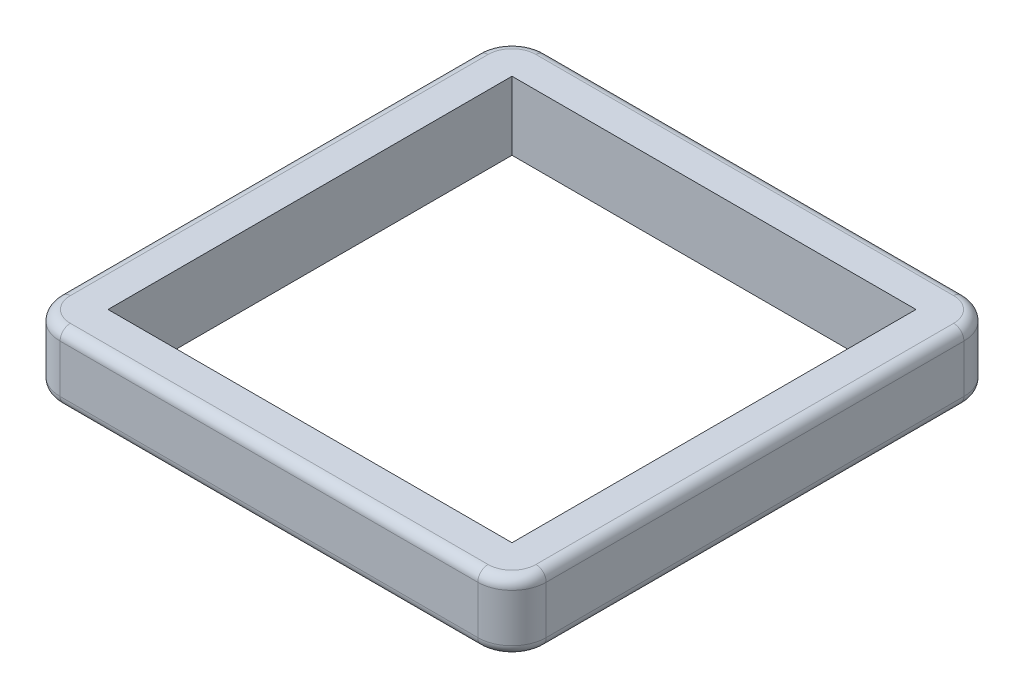
SolidWorks part; units mm, degrees
ref_plane "Front Plane" through (0, 0, 0) normal (0, 0, 1) x (1, 0, 0)
ref_plane "Top Plane" through (0, 0, 0) normal (0, 1, 0) x (1, 0, 0)
ref_plane "Right Plane" through (0, 0, 0) normal (1, 0, 0) x (0, 0, -1)
sketch "Sketch1" plane through (0, 0, 0) normal (0, 1, 0) x (1, 0, 0)
  line L0 (-450.85, 450.85) -> (450.85, 450.85)
  line L1 (-374.65, 374.65) -> (374.65, 374.65)
  line L2 (-374.65, 374.65) -> (-374.65, -374.65)
  line L3 (-374.65, -374.65) -> (374.65, -374.65)
  line L4 (374.65, 374.65) -> (374.65, -374.65)
  line L5 (-374.65, 374.65) -> (374.65, -374.65) construction
  line L6 (-374.65, -374.65) -> (374.65, 374.65) construction
  line L7 (450.85, 450.85) -> (450.85, -450.85)
  line L8 (-450.85, -450.85) -> (450.85, -450.85)
  line L9 (-450.85, 450.85) -> (-450.85, -450.85)
  point P0 (0, 0)
  dimension "D1" = 749.3
  dimension "D2" = 76.2
extrude "Boss-Extrude1" add sketch "Sketch1" along normal blind 127
fillet "Fillet1" radius 63.5 4 edges at (-450.85, 63.5, -450.85) (450.85, 63.5, -450.85) (450.85, 63.5, 450.85) (-450.85, 63.5, 450.85)
fillet "Fillet2" radius 19.05 16 edges at (432.2513, 0, 432.2513) (0, 0, 450.85) (-432.2513, 0, 432.2513) (-450.85, 0, 0) (-432.2513, 0, -432.2513) (0, 0, -450.85) (432.2513, 0, -432.2513) (432.2513, 127, 432.2513) (0, 127, 450.85) (-432.2513, 127, 432.2513) (-450.85, 127, 0) (-432.2513, 127, -432.2513) (0, 127, -450.85) (432.2513, 127, -432.2513) (450.85, 0, 0) (450.85, 127, 0)
